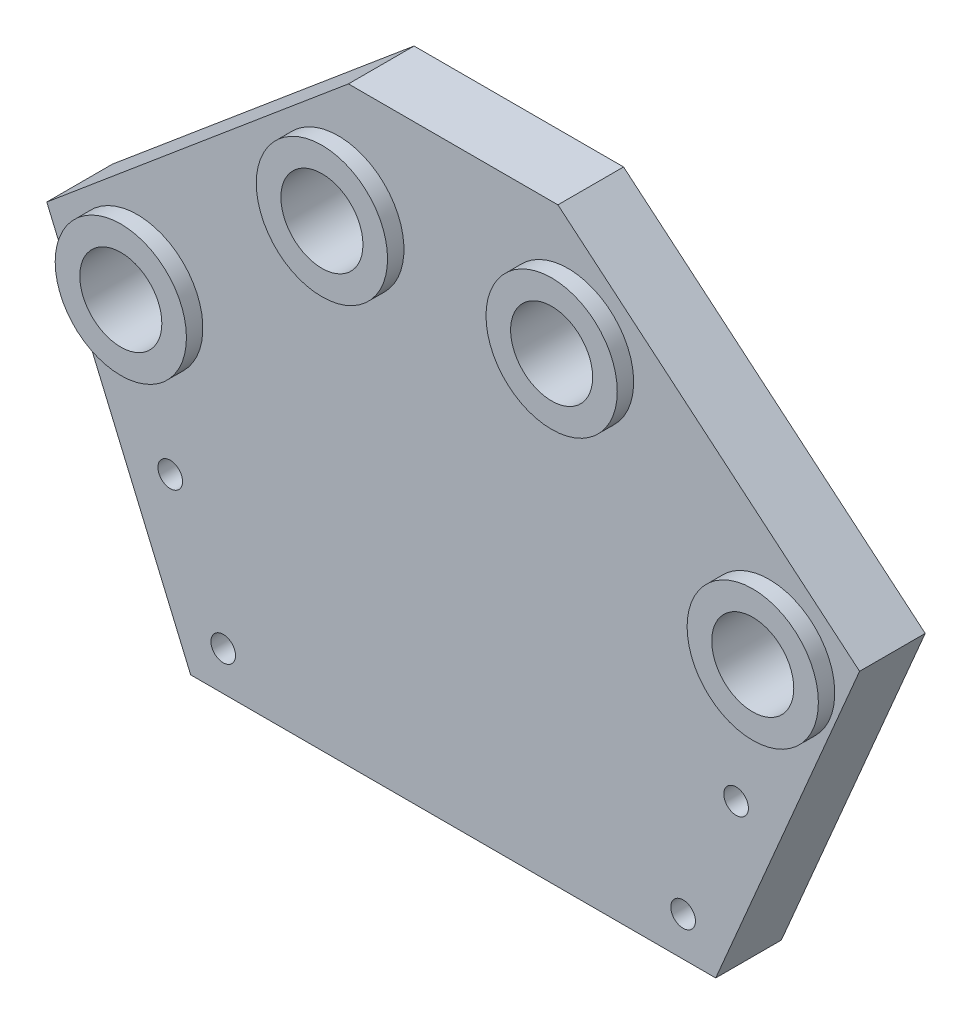
SolidWorks part; units mm, degrees
ref_plane "Front Plane" through (0, 0, 0) normal (0, 0, 1) x (1, 0, 0)
ref_plane "Top Plane" through (0, 0, 0) normal (0, 1, 0) x (1, 0, 0)
ref_plane "Right Plane" through (0, 0, 0) normal (1, 0, 0) x (0, 0, -1)
sketch "Sketch1" plane through (0, 0, 0) normal (0, 0, 1) x (1, 0, 0)
  line L0 (0, 0) -> (0, 62.6202) construction
  line L3 (-25.4, 0) -> (25.4, 0)
  line L4 (55, 0) -> (-55, 0) construction
  line L5 (25.4, 0) -> (39.3204, 32.6598)
  line L7 (-25.4, 0) -> (-39.3204, 32.6598)
  line L8 (39.3204, 32.6598) -> (10.1341, 57.15)
  line L9 (-39.3204, 32.6598) -> (-10.1341, 57.15)
  line L10 (10.1341, 57.15) -> (-10.1341, 57.15)
  line L11 (16.2146, 52.0479) -> (13.3878, 48.679) construction
  line L12 (-16.2146, 52.0479) -> (-13.3878, 48.679) construction
  line L13 (35.6722, 35.7211) -> (23.9079, 21.701) construction
  line L14 (-35.6722, 35.7211) -> (-23.9079, 21.701) construction
  circle A4 centre (11.1125, 45.9674) radius 3.9688
  circle A5 centre (-11.1125, 45.9674) radius 3.9688
  circle A6 centre (30.57, 29.6406) radius 3.9687
  circle A7 centre (-30.57, 29.6406) radius 3.9688
  point P9 (0, 0)
  point P15 (0, 57.15)
  dimension "D6" = 4.7625
  dimension "D8" = 7.9375
  dimension "D1" = 50.8
  dimension "D2" = 22.225
  dimension "D3" = 38.1
  dimension "D4" = 40
  dimension "D5" = 57.15
  dimension "D7" = 25.4
  dimension "D9" = 7.9375
  dimension "D10" = 7.9375
extrude "Boss-Extrude1" add sketch "Sketch1" along normal blind 6.35
sketch "Sketch2" plane through (0, 0, 0) normal (0, 0, -1) x (-1, 0, 0)
  line L0 (-15.875, 0) -> (-23.3444, 17.5246) construction
  line L1 (25.4, 0) -> (-25.4, 0) construction
  line L3 (0, 0) -> (0, 25.9423) construction
  line L4 (-25.4, 0) -> (-39.3204, 32.6598) construction
  line L5 (-23.3444, 17.5246) -> (-31.4051, 14.0889) construction
  line L7 (-25.4, 0) -> (-27.8898, 5.8415) construction
  line L8 (-27.8898, 5.8415) -> (-19.8292, 9.2772) construction
  line L9 (-19.8292, 9.2772) -> (-15.875, 0) construction
  line L10 (-26.6449, 2.9208) -> (-17.8521, 4.6386) construction
  circle A4 centre (-27.3747, 15.8067) radius 1.1906
  circle A5 centre (-22.2485, 3.7797) radius 1.1906
  circle A6 centre (22.2485, 3.7797) radius 1.1906
  circle A7 centre (27.3747, 15.8067) radius 1.1906
  dimension "D3" = 6.35
  dimension "D4" = 2.3813
  dimension "D1" = 9.525
  dimension "D2" = 19.05
extrude "Cut-Extrude1" cut sketch "Sketch2" against normal up to surface (6.35 mm away) up to face at (0, 29.9366, 6.35)
sketch "Sketch3" plane through (0, 0, 6.35) normal (0, 0, 1) x (1, 0, 0)
  circle A0 centre (-11.1125, 45.9674) radius 6.35
  circle A1 centre (11.1125, 45.9674) radius 6.35
  circle A2 centre (-30.57, 29.6406) radius 6.35
  circle A3 centre (30.57, 29.6406) radius 6.35
  circle A4 centre (30.57, 29.6406) radius 3.9688 construction
  circle A5 centre (11.1125, 45.9674) radius 3.9688 construction
  circle A6 centre (-11.1125, 45.9674) radius 3.9688 construction
  circle A7 centre (-30.57, 29.6406) radius 3.9688 construction
  circle A8 centre (30.57, 29.6406) radius 3.9687
  circle A9 centre (11.1125, 45.9674) radius 3.9688
  circle A10 centre (-11.1125, 45.9674) radius 3.9688
  circle A11 centre (-30.57, 29.6406) radius 3.9688
  dimension "D1" = 12.7
extrude "Boss-Extrude2" add sketch "Sketch3" along normal blind 1.5875
